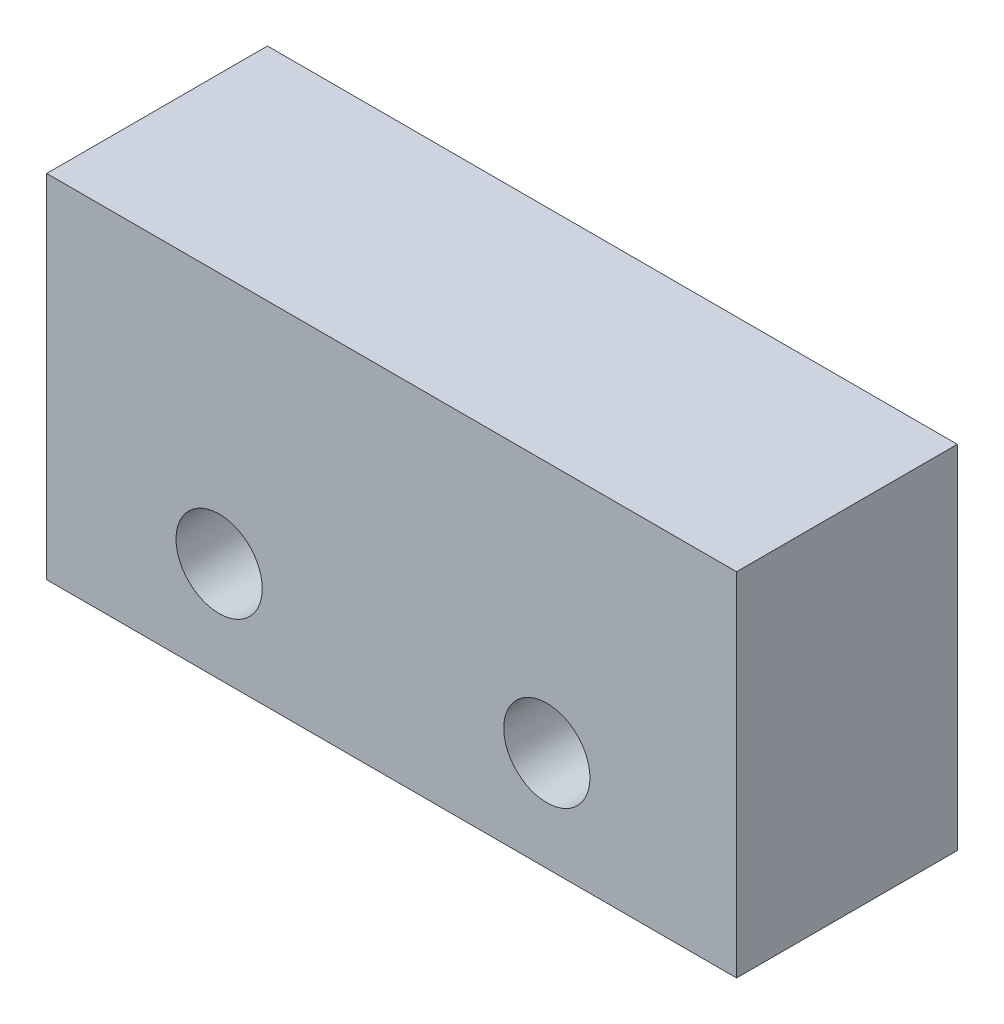
SolidWorks part; units mm, degrees
ref_plane "Front Plane" through (0, 0, 0) normal (0, 0, 1) x (1, 0, 0)
ref_plane "Top Plane" through (0, 0, 0) normal (0, 1, 0) x (1, 0, 0)
ref_plane "Right Plane" through (0, 0, 0) normal (1, 0, 0) x (0, 0, -1)
sketch "Sketch1" plane through (0, 0, 0) normal (0, 0, 1) x (1, 0, 0)
  line L1 (10, -5.1) -> (-10, -5.1)
  line L2 (10, -5.1) -> (10, 5.1)
  line L3 (10, 5.1) -> (-10, 5.1)
  line L4 (-10, -5.1) -> (-10, 5.1)
  line L5 (10, -5.1) -> (-10, 5.1) construction
  line L6 (10, 5.1) -> (-10, -5.1) construction
  point P0 (0, 0)
  dimension "D1" = 20
  dimension "D2" = 10.2
extrude "Boss-Extrude1" add sketch "Sketch1" along normal mid plane 6.4
sketch "Sketch3" plane through (0, 0, 3.2) normal (0, 0, 1) x (1, 0, 0)
  line L0 (-5, -2.2) -> (4.5, -2.2) construction
  line L1 (-10, 5.1) -> (-10, -5.1) construction
  line L3 (-10, -5.1) -> (10, -5.1) construction
  circle A0 centre (4.5, -2.2) radius 1.25
  circle A1 centre (-5, -2.2) radius 1.25
  dimension "D4" = 2.5
  dimension "D1" = 14.5
  dimension "D2" = 9.5
  dimension "D3" = 2.9
extrude "Cut-Extrude1" cut sketch "Sketch3" against normal through all
